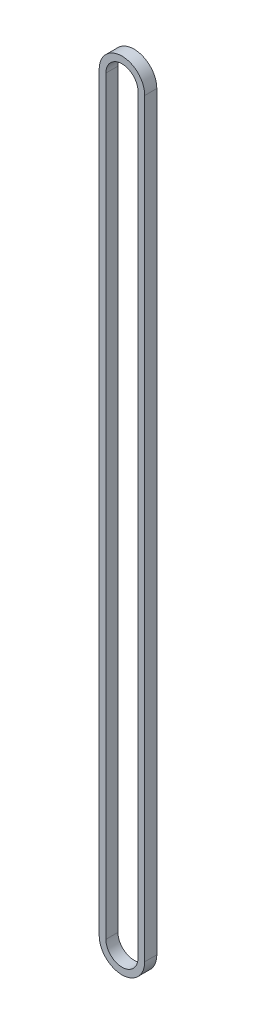
SolidWorks part; units mm, degrees
material "Найлон 6/10"
ref_plane "Спереди" through (0, 0, 0) normal (0, 0, 1) x (1, 0, 0)
ref_plane "Сверху" through (0, 0, 0) normal (0, 1, 0) x (1, 0, 0)
ref_plane "Справа" through (0, 0, 0) normal (1, 0, 0) x (0, 0, -1)
sketch "Эскиз1" plane through (0, 0, 0) normal (0, 0, 1) x (1, 0, 0)
  line L0 (0, -140) -> (0, 140) construction
  line L1 (-8.5, -140) -> (-8.5, 140)
  line L2 (8.5, -140) -> (8.5, 140)
  line L3 (0, -140) -> (0, 140) construction
  line L4 (-6, -140) -> (-6, 140)
  line L5 (6, -140) -> (6, 140)
  arc A0 (-8.5, -140) -> (8.5, -140) centre (0, -140) ccw
  arc A1 (8.5, 140) -> (-8.5, 140) centre (0, 140) ccw
  arc A2 (-6, -140) -> (6, -140) centre (0, -140) ccw
  arc A3 (6, 140) -> (-6, 140) centre (0, 140) ccw
  point P3 (0, 0)
  point P10 (0, 0)
  dimension "D1" = 280
  dimension "D2" = 17
  dimension "D3" = 2.5
extrude "Бобышка-Вытянуть1" add sketch "Эскиз1" along normal blind 4.5
